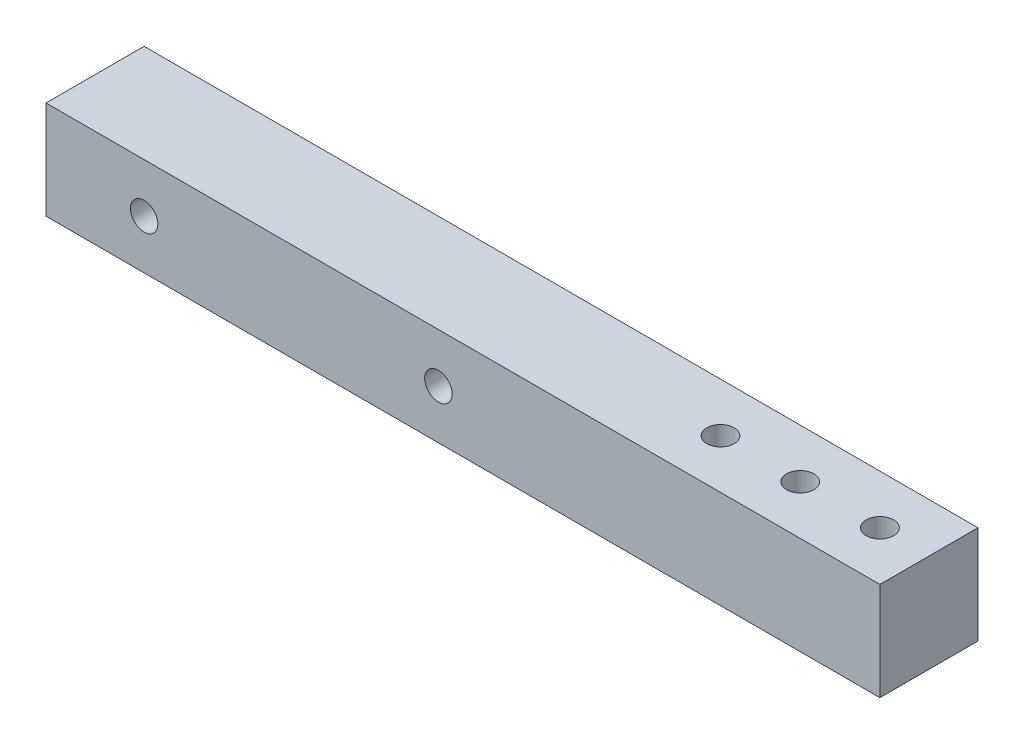
SolidWorks part; units mm, degrees
ref_plane "Front Plane" through (0, 0, 0) normal (0, 0, 1) x (1, 0, 0)
ref_plane "Top Plane" through (0, 0, 0) normal (0, 1, 0) x (1, 0, 0)
ref_plane "Right Plane" through (0, 0, 0) normal (1, 0, 0) x (0, 0, -1)
sketch "Sketch1" plane through (0, 0, 0) normal (0, 0, 1) x (1, 0, 0)
  line L1 (0, 0) -> (107.95, 0)
  line L2 (0, 0) -> (0, 12.7)
  line L3 (0, 12.7) -> (107.95, 12.7)
  line L4 (107.95, 0) -> (107.95, 12.7)
  point P7 (0, 12.7)
  dimension "D1" = 12.7
  dimension "D2" = 107.95
extrude "Boss-Extrude1" add sketch "Sketch1" along normal blind 12.7
sketch "Sketch2" plane through (0, 12.7, 0) normal (0, 1, 0) x (1, 0, 0)
  line L0 (107.95, 0) -> (0, 0) construction
  line L1 (107.95, -12.7) -> (101.6, -12.7)
  line L2 (107.95, -12.7) -> (107.95, 0)
  line L3 (107.95, 0) -> (101.6, 0)
  line L4 (101.6, -12.7) -> (101.6, 0)
  line L5 (80.9625, -12.7) -> (80.9625, 0) construction
  line L7 (101.6, -12.7) -> (101.6, 0)
  line L8 (101.6, 0) -> (91.575, 0)
  line L10 (107.95, -12.7) -> (80.9625, -12.7)
  line L11 (107.95, -12.7) -> (0, -12.7) construction
  circle A1 centre (101.6, -6.35) radius 1.778
  circle A2 centre (80.9625, -6.35) radius 1.778
  dimension "D3" = 3.556
  dimension "D2" = 3.556
  dimension "D1" = 6.35
  dimension "D4" = 26.9875
extrude "Cut-Extrude1" cut sketch "Sketch2" against normal up to surface (12.7 mm away) contours L5 A2 | A2 L5 | A1
sketch "Sketch3" plane through (0, 0, 0) normal (0, -1, 0) x (1, 0, 0)
  line L0 (80.9625, 6.35) -> (101.6, 6.35) construction
  circle A0 centre (91.2812, 6.35) radius 1.778
  dimension "D1" = 3.556
extrude "Cut-Extrude2" cut sketch "Sketch3" against normal up to surface (12.7 mm away) up to face at (80.9625, 12.7, 8.128)
sketch "Sketch4" plane through (0, 0, 0) normal (0, 0, -1) x (-1, 0, 0)
  line L0 (0, 0) -> (-12.7, 0) construction
  line L1 (0, 0) -> (-107.95, 0) construction
  line L2 (-12.7, 0) -> (-12.7, 12.7) construction
  line L3 (-107.95, 12.7) -> (0, 12.7) construction
  line L4 (0, 0) -> (-50.8, 0) construction
  line L5 (-50.8, 0) -> (-50.8, 12.7) construction
  circle A0 centre (-12.7, 6.35) radius 1.778
  circle A1 centre (-50.8, 6.35) radius 1.778
  dimension "D3" = 3.556
  dimension "D4" = 3.556
  dimension "D1" = 12.7
  dimension "D2" = 50.8
extrude "Cut-Extrude3" cut sketch "Sketch4" against normal up to surface (12.7 mm away) contours A0 | A1 up to face at (53.975, 6.35, 12.7)
